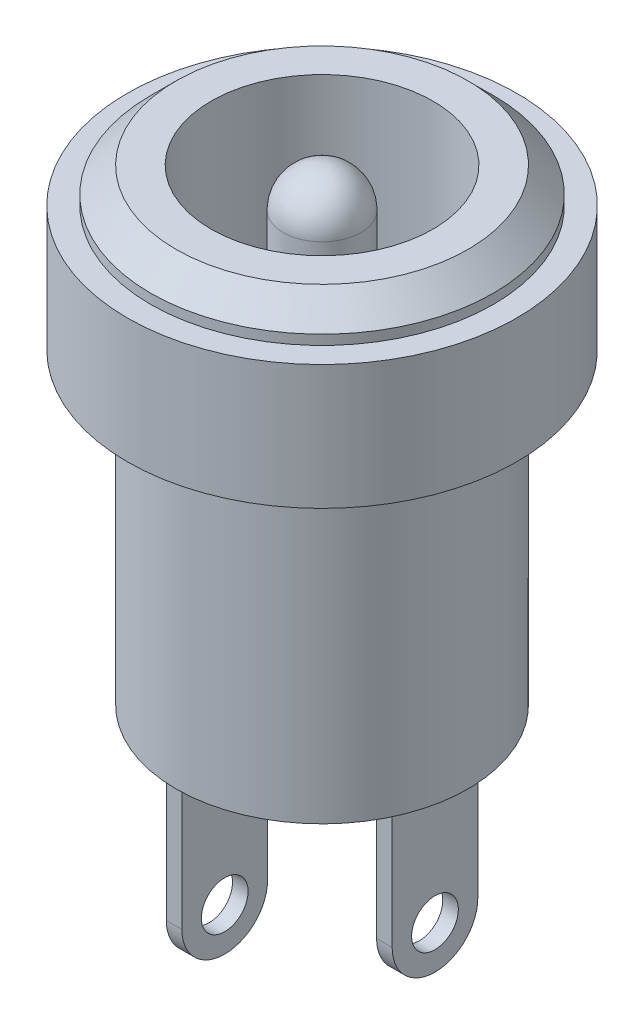
SolidWorks part; units mm, degrees
ref_plane "Plan de face" through (0, 0, 0) normal (0, 0, 1) x (1, 0, 0)
ref_plane "Plan de dessus" through (0, 0, 0) normal (0, 1, 0) x (1, 0, 0)
ref_plane "Plan de droite" through (0, 0, 0) normal (1, 0, 0) x (0, 0, -1)
sketch "Esquisse1" plane through (0, 0, 0) normal (0, 0, 1) x (1, 0, 0)
  line L0 (0, 6) -> (0, -6) construction
  line L1 (0, -6) -> (-3.75, -6)
  line L2 (-3.75, -6) -> (-3.75, 1.9)
  line L3 (-3.75, 1.9) -> (-5, 1.9)
  line L4 (-5, 1.9) -> (-5, 5.1)
  line L5 (-5, 5.1) -> (-4.4, 5.1)
  line L6 (0, 6) -> (-3.75, 6)
  line L7 (-4.4, 5.1) -> (-4.4, 5.35)
  line L8 (0, 6) -> (0, -6)
  line L9 (-4.4, 5.35) -> (-3.75, 6)
  dimension "D1" = 12
  dimension "D2" = 7.9
  dimension "D3" = 3.2
  dimension "D4" = 0.6
  dimension "D5" = 0.25
  dimension "D6" = 3.75
  dimension "D7" = 5
  dimension "D8" = 135
revolve "Révolution1" add sketch "Esquisse1" angle 360 about L0
sketch "Esquisse2" plane through (0, 6, 0) normal (0, 1, 0) x (1, 0, 0)
  circle A0 centre (0, 0) radius 2.85
  circle A1 centre (0, 0) radius 1
  dimension "D1" = 5.7
  dimension "D2" = 2
extrude "Enlèv. mat.-Extru.1" cut sketch "Esquisse2" against normal blind 10
fillet "Congé1" radius 1 1 edges at (0, 6, 1)
sketch "Esquisse3" plane through (0, -6, 0) normal (0, -1, 0) x (1, 0, 0)
  line L1 (-2.9, 1.1) -> (-2.5, 1.1)
  line L2 (-2.9, 1.1) -> (-2.9, -1.1)
  line L3 (-2.9, -1.1) -> (-2.5, -1.1)
  line L4 (-2.5, 1.1) -> (-2.5, -1.1)
  line L5 (-2.9, 1.1) -> (-2.5, -1.1) construction
  line L6 (-2.9, -1.1) -> (-2.5, 1.1) construction
  line L7 (2.5, 1.1) -> (2.9, 1.1)
  line L8 (2.5, 1.1) -> (2.5, -1.1)
  line L9 (2.5, -1.1) -> (2.9, -1.1)
  line L10 (2.9, 1.1) -> (2.9, -1.1)
  line L11 (2.5, 1.1) -> (2.9, -1.1) construction
  line L12 (2.5, -1.1) -> (2.9, 1.1) construction
  point P0 (-2.7, 0)
  point P5 (2.7, 0)
  dimension "D1" = 0.4
  dimension "D2" = 0.4
  dimension "D3" = 2.2
  dimension "D4" = 2.2
  dimension "D5" = 5
  dimension "D6" = 2.5
extrude "Boss.-Extru.1" add sketch "Esquisse3" along normal blind 6.8
sketch "Esquisse4" plane through (2.9, 0, 0) normal (1, 0, 0) x (0, 0, -1)
  line L0 (-1.1, -9.4) -> (1.1, -9.4) construction
  line L1 (-1.1, -12.8) -> (-1.1, -6) construction
  line L2 (1.1, -12.8) -> (1.1, -6) construction
  line L3 (-1.1, -9.4) -> (-1.1, -12.8)
  line L4 (-1.1, -12.8) -> (1.1, -12.8)
  line L5 (1.1, -12.8) -> (1.1, -9.4)
  line L6 (1.1, -6) -> (-1.1, -6) construction
  arc A0 (-1.1, -9.4) -> (1.1, -9.4) centre (0, -9.4) ccw
  circle A1 centre (0, -9.4) radius 0.6
  line M2 (-1.1, -6) -> (-1.1, -12.8)
  line M3 (-1.1, -12.8) -> (1.1, -12.8)
  line M4 (1.1, -12.8) -> (1.1, -6)
  dimension "D1" = 3.4
  dimension "D2" = 1.2
extrude "Enlèv. mat.-Extru.2" cut sketch "Esquisse4" against normal up to next contours A0 M2 M3 M4 | A1
sketch "Esquisse6" plane through (-2.9, 0, 0) normal (-1, 0, 0) x (0, 0, 1)
  line L0 (-1.1, -12.8) -> (-1.1, -6) construction
  line L1 (1.1, -12.8) -> (1.1, -6) construction
  line L2 (-1.1, -11.7) -> (1.1, -11.7) construction
  line L3 (1.1, -12.8) -> (-1.1, -12.8) construction
  line L4 (-1.1, -11.7) -> (-1.1, -12.8)
  line L5 (-1.1, -12.8) -> (1.1, -12.8)
  line L6 (1.1, -12.8) -> (1.1, -11.7)
  arc A0 (-1.1, -11.7) -> (1.1, -11.7) centre (0, -11.7) ccw
  circle A1 centre (0, -11.7) radius 0.6
  line M2 (-1.1, -6) -> (-1.1, -12.8)
  line M3 (-1.1, -12.8) -> (1.1, -12.8)
  line M4 (1.1, -12.8) -> (1.1, -6)
  dimension "D2" = 1.2
  dimension "D1" = 1.1
extrude "Enlèv. mat.-Extru.3" cut sketch "Esquisse6" against normal up to next contours A0 M2 M3 | A0 L5 M4 | A1
